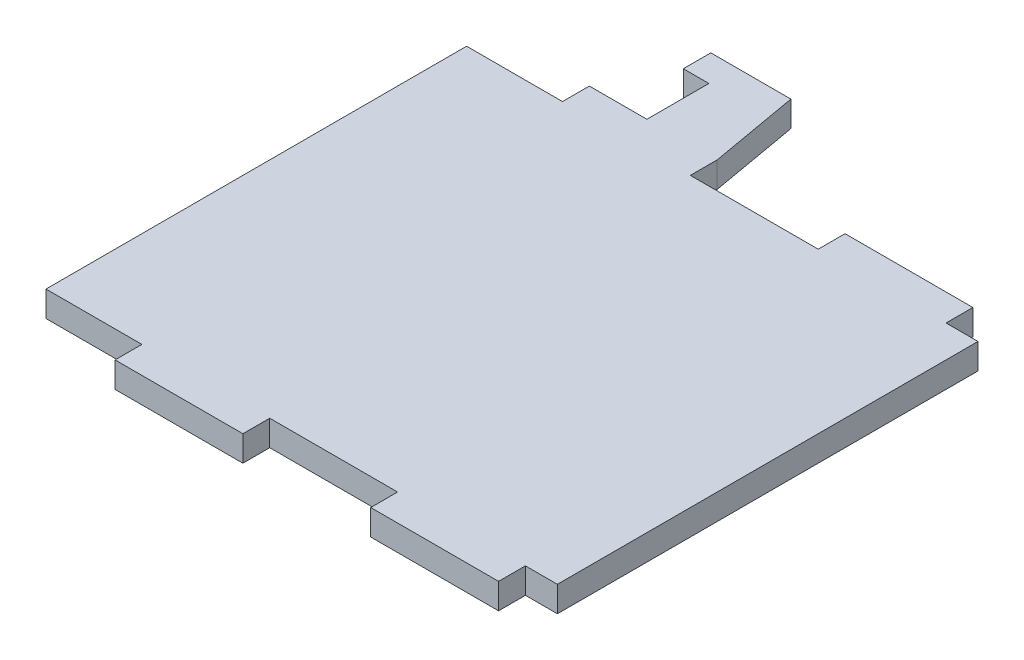
SolidWorks part; units mm, degrees
ref_plane "Plan de face" through (0, 0, 0) normal (0, 0, 1) x (1, 0, 0)
ref_plane "Plan de dessus" through (0, 0, 0) normal (0, 1, 0) x (1, 0, 0)
ref_plane "Plan de droite" through (0, 0, 0) normal (1, 0, 0) x (0, 0, -1)
sketch "Esquisse1" plane through (0, 0, 0) normal (0, 1, 0) x (1, 0, 0)
  line L1 (0, 0) -> (15, 0)
  line L2 (0, 0) -> (0, 65.8)
  line L3 (0, 65.8) -> (15, 65.8)
  line L4 (80, 0) -> (80, 65.8)
  line L5 (55, 0) -> (55, 65.8) construction
  line L6 (75, 65.8) -> (75, 0) construction
  line L7 (15, 65.8) -> (15, 70)
  line L8 (35, 65.8) -> (35, 70)
  line L10 (35, 65.8) -> (55, 65.8)
  line L12 (75, 70) -> (55, 70)
  line L13 (55, 65.8) -> (55, 70)
  line L14 (75, 65.8) -> (75, 70)
  line L16 (75, 0) -> (75, -4.2)
  line L17 (55, 0) -> (55, -4.2)
  line L18 (75, -4.2) -> (55, -4.2)
  line L19 (15, -4.2) -> (35, -4.2)
  line L20 (35, 0) -> (35, -4.2)
  line L21 (15, 0) -> (15, -4.2)
  line L22 (75, 65.8) -> (80, 65.8)
  line L23 (75, 0) -> (80, 0)
  line L24 (35, 0) -> (55, 0)
  line L25 (24, 70) -> (24, 79.7)
  line L26 (24, 79.7) -> (20, 79.7)
  line L27 (20, 79.7) -> (20, 84)
  line L28 (20, 84) -> (32.5314, 84)
  line L29 (32.5314, 84) -> (35, 70)
  line L30 (24, 70) -> (15, 70)
  line L31 (35, 70) -> (55, 70) construction
  line L32 (35, 65.8) -> (35, 0) construction
  line L33 (15, 65.8) -> (15, 0) construction
  line L34 (24, 70) -> (35, 70) construction
  line L35 (35, -4.2) -> (55, -4.2) construction
  point P0 (0, 0)
  point P12 (45, 65.8)
  point P13 (65, 70)
  dimension "D1" = 20
  dimension "D2" = 4.2
  dimension "D3" = 65.8
  dimension "D4" = 80
  dimension "D5" = 15
  dimension "D6" = 9.7
  dimension "D7" = 4
  dimension "D8" = 4.3
  dimension "D9" = 20
  dimension "D10" = 5
  dimension "D11" = 9
extrude "Boss.-Extru.1" add sketch "Esquisse1" along normal blind 4
sketch "Sketch1" plane through (0, 4, 0) normal (0, 1, 0) x (1, 0, 0)
  line L0 (80, 63.8) -> (70, 57.9)
  line L1 (80, 0) -> (80, 65.8) construction
  line L2 (70, 57.9) -> (70, 7.9)
  line L3 (70, 7.9) -> (80, 2)
  line L4 (80, 2) -> (80, 63.8)
  line L5 (80, 63.8) -> (70, 63.8) construction
  line L6 (70, 63.8) -> (70, 57.9) construction
  line L7 (80, 2) -> (70, 2) construction
  line L8 (70, 2) -> (70, 7.9) construction
  line L9 (70, 32.9) -> (0, 32.9) construction
  line L10 (0, 65.8) -> (0, 0) construction
  line L11 (80, 65.8) -> (75, 65.8) construction
  dimension "D1" = 2
  dimension "D2" = 50
  dimension "D3" = 10
extrude "Cut-Extrude1" [suppressed] cut sketch "Sketch1" against normal through all
